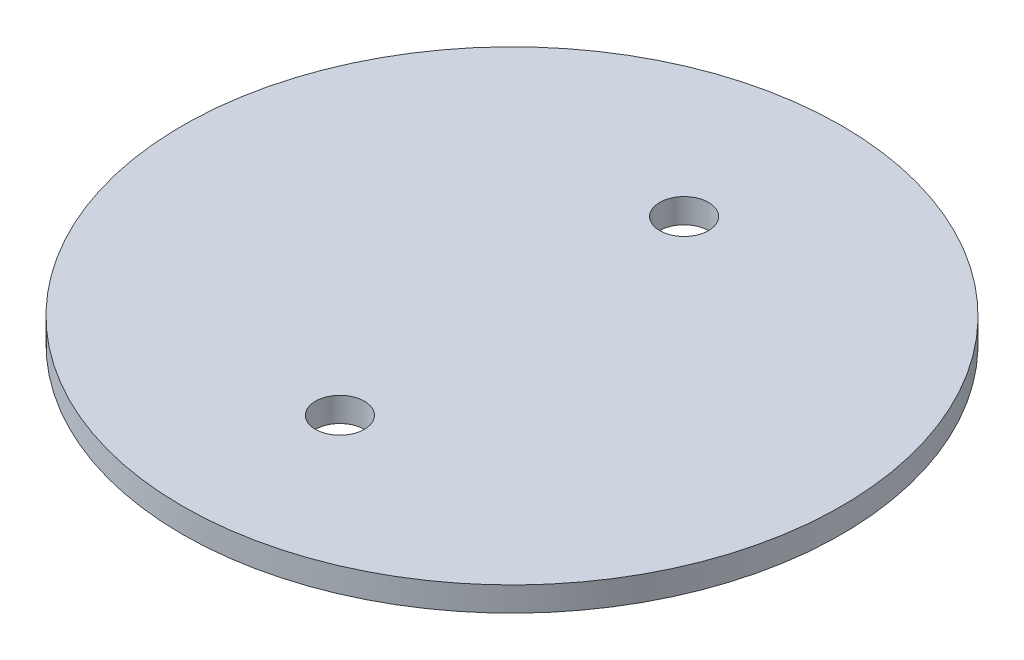
SolidWorks part; units mm, degrees
ref_plane "Front Plane" through (0, 0, 0) normal (0, 0, 1) x (1, 0, 0)
ref_plane "Top Plane" through (0, 0, 0) normal (0, 1, 0) x (1, 0, 0)
ref_plane "Right Plane" through (0, 0, 0) normal (1, 0, 0) x (0, 0, -1)
sketch "Sketch1" plane through (0, 0, 0) normal (0, 1, 0) x (1, 0, 0)
  line L0 (0, 0) -> (0, -22.352)
  line L1 (0, 0) -> (11.2463, 0)
  circle A0 centre (0, 0) radius 42.799
  circle A1 centre (0, -22.352) radius 3.175
  circle A2 centre (0, 22.352) radius 3.175
  dimension "D1" = 22.352
  dimension "D2" = 6.35
  dimension "D3" = 85.598
extrude "Boss-Extrude1" add sketch "Sketch1" along normal blind 3.175
